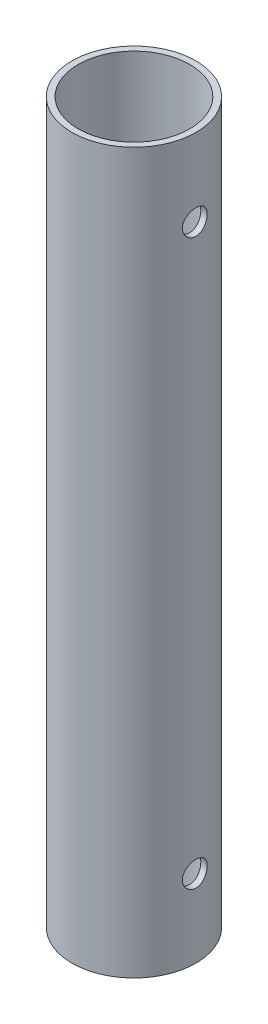
SolidWorks part; units mm, degrees
ref_plane "Front" through (0, 0, 0) normal (0, 0, 1) x (1, 0, 0)
ref_plane "Top" through (0, 0, 0) normal (0, 1, 0) x (1, 0, 0)
ref_plane "Right" through (0, 0, 0) normal (1, 0, 0) x (0, 0, -1)
sketch "Sketch1" plane through (0, 0, 0) normal (0, 1, 0) x (1, 0, 0)
  circle A0 centre (0, 0) radius 10
  circle A1 centre (0, 0) radius 9
  dimension "D1" = 20
  dimension "D2" = 1
extrude "Boss-Extrude1" add sketch "Sketch1" along normal blind 116
ref_plane "Plane1" through (10, 0, 0) normal (1, 0, 0) x (0, 0, -1)
sketch "Sketch3" plane through (10, 0, 0) normal (1, 0, 0) x (0, 0, -1)
  line L0 (0, 116) -> (0, 103.5) construction
  line L1 (9, 116) -> (-9, 116) construction
  line L2 (0, 0) -> (0, 12.5) construction
  circle A0 centre (0, 103.5) radius 2
  circle A1 centre (0, 12.5) radius 2
  dimension "D3" = 4
  dimension "D4" = 4
  dimension "D1" = 12.5
  dimension "D2" = 12.5
extrude "Cut-Extrude2" cut sketch "Sketch3" against normal through all
